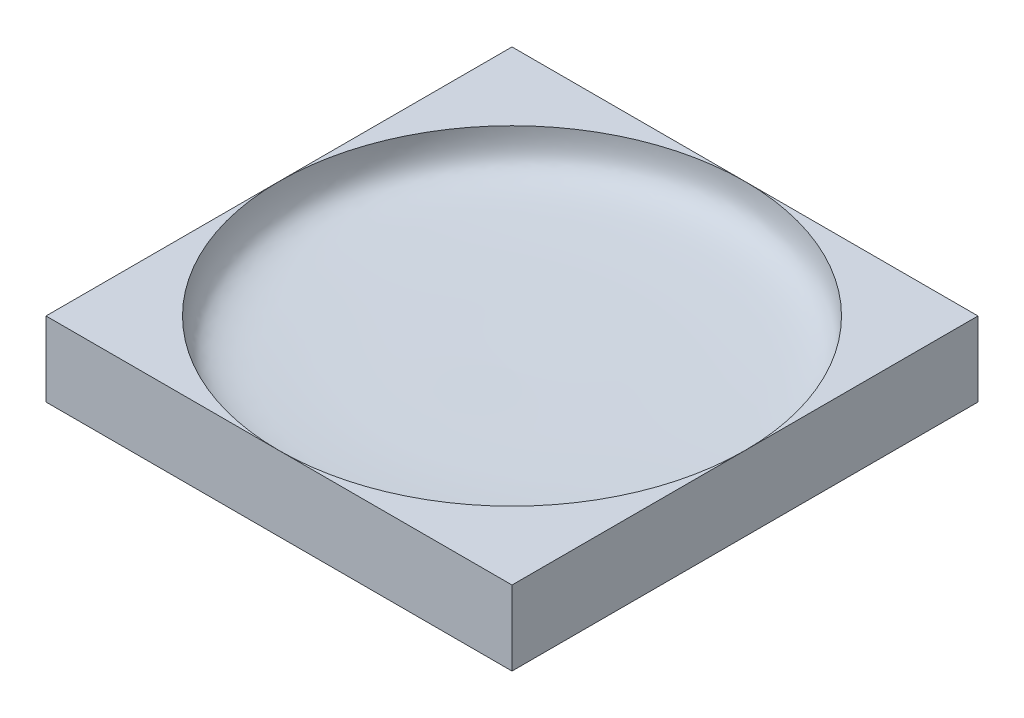
SolidWorks part; units mm, degrees
ref_plane "Front Plane" through (0, 0, 0) normal (0, 0, 1) x (1, 0, 0)
ref_plane "Top Plane" through (0, 0, 0) normal (0, 1, 0) x (1, 0, 0)
ref_plane "Right Plane" through (0, 0, 0) normal (1, 0, 0) x (0, 0, -1)
sketch "Sketch1" plane through (0, 0, 0) normal (0, 1, 0) x (1, 0, 0)
  line L1 (-125, 125) -> (125, 125)
  line L2 (-125, 125) -> (-125, -125)
  line L3 (-125, -125) -> (125, -125)
  line L4 (125, 125) -> (125, -125)
  dimension "D1" = 250
  dimension "D2" = 250
  dimension "D3" = 125
  dimension "D4" = 125
extrude "Boss-Extrude1" add sketch "Sketch1" along normal blind 40
sketch "Sketch2" plane through (0, 0, 0) normal (0, 0, 1) x (1, 0, 0)
  line L0 (0, 59.2239) -> (0, -74.7925) construction
  line L1 (125, 56.4735) -> (125, -39.8773) construction
  line L3 (-125, 40) -> (125, 40) construction
  line L4 (0, 15) -> (0, 63.1162)
  line L5 (0, 63.1162) -> (125, 40)
  line L6 (168.61, 15) -> (-169.5385, 15) construction
  spline S0 degree 3 poles (0, 15) (48.1962, 15.8824) (65.9596, 14.6973) (121.0329, 18.9179) (125, 29.7122) (125, 40) knots 0 0 0 0 0.694216 0.861706 1 1 1 1
  dimension "D1" = 125
revolve "Cut-Revolve2" cut sketch "Sketch2" angle 360 about L4
